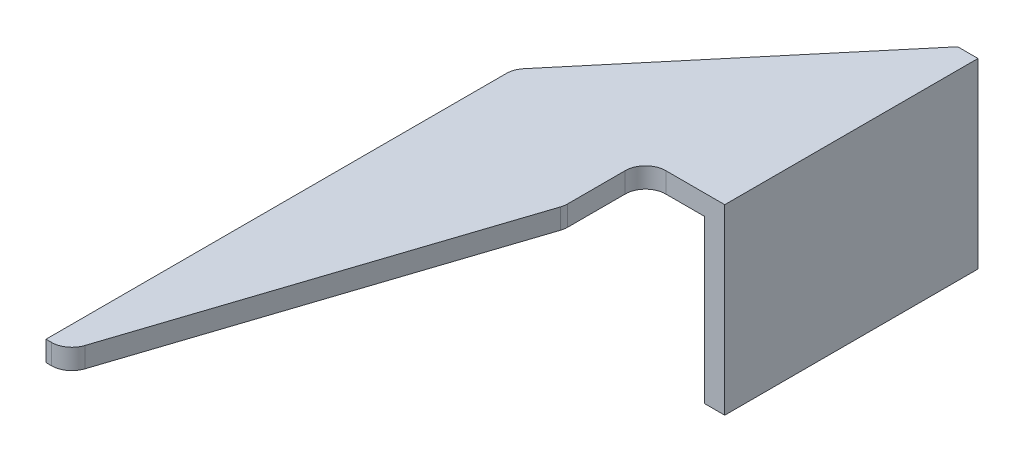
SolidWorks part; units mm, degrees
ref_plane "Front Plane" through (0, 0, 0) normal (0, 0, 1) x (1, 0, 0)
ref_plane "Top Plane" through (0, 0, 0) normal (0, 1, 0) x (1, 0, 0)
ref_plane "Right Plane" through (0, 0, 0) normal (1, 0, 0) x (0, 0, -1)
sketch "Sketch1" plane through (0, 0, 0) normal (0, 0, 1) x (1, 0, 0)
  line L0 (0, 0) -> (0, 16)
  line L1 (0, 16) -> (-20, 16)
  dimension "D1" = 16
  dimension "D2" = 20
extrude "Extrude-Thin1" add sketch "Sketch1" along normal blind 70 thin
ref_plane "Plane1" through (-20, 0, 0) normal (1, 0, 0) x (0, 0, -1)
sketch "Sketch2" plane through (0, 18, 0) normal (0, 1, 0) x (1, 0, 0)
  line L0 (2, -25) -> (-5.822, -25)
  line L1 (2, -70) -> (2, 0) construction
  line L2 (-5.822, -25) -> (-5.822, -33)
  line L3 (2, -70) -> (-20, -70) construction
  line L4 (2, -25) -> (2, -70)
  line L5 (2, -70) -> (-18, -70)
  line L6 (2, 0) -> (-20, 0) construction
  line L8 (-5.822, -33) -> (-18, -70)
  dimension "D1" = 25
  dimension "D2" = 7.822
  dimension "D3" = 2
  dimension "D4" = 8
extrude "Cut-Extrude1" cut sketch "Sketch2" against normal through all
sketch "Sketch3" plane through (0, 18, 0) normal (0, 1, 0) x (1, 0, 0)
  line L0 (-20, -23.8351) -> (0, 0)
  line L1 (-20, -70) -> (-20, 0) construction
  line L3 (0, 0) -> (0, 5.106) construction
  line L4 (2, 0) -> (-20, 0) construction
  line L5 (-20, -23.8351) -> (-20, 0)
  line L6 (-20, 0) -> (0, 0)
  dimension "D1" = 50
extrude "Cut-Extrude2" cut sketch "Sketch3" against normal through all
fillet "Fillet1" radius 2 4 edges at (-5.822, 17, 25) (-5.822, 17, 33) (-18, 17, 70) (-20, 17, 23.8351)
